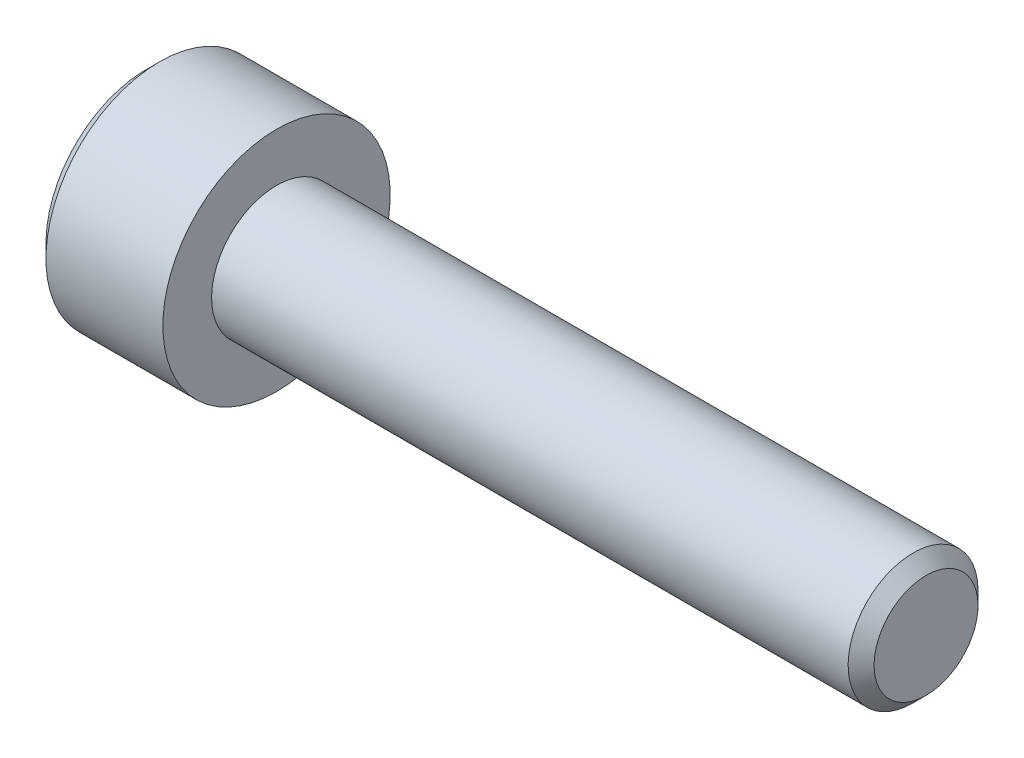
SolidWorks part; units mm, degrees
ref_plane "Front" through (0, 0, 0) normal (0, 0, 1) x (1, 0, 0)
ref_plane "Top" through (0, 0, 0) normal (0, 1, 0) x (1, 0, 0)
ref_plane "Right" through (0, 0, 0) normal (1, 0, 0) x (0, 0, -1)
ref_plane "Plane1" through (0, 0, 0) normal (0, 0, 1) x (1, 0, 0)
sketch "Sketch1" plane through (0, 0, 0) normal (0, 0, 1) x (1, 0, 0)
  line L0 (-4, 0) -> (-4, 3.1)
  line L1 (-4, 3.1) -> (-3.6, 3.5)
  line L2 (-3.6, 3.5) -> (0, 3.5)
  line L3 (0, 3.5) -> (0, 2)
  line L4 (0, 2) -> (20, 2)
  line L6 (20, 2) -> (20, 0)
  line L7 (20, 0) -> (-4, 0)
  line L8 (20, 0) -> (-4, 0) construction
  dimension "D1" = 20
  dimension "D2" = 4
  dimension "D3" = 2
  dimension "D4" = 3.5
revolve "Revolve1" add sketch "Sketch1" angle 360 about L8
ref_plane "Plane2" through (0, 0, 0) normal (0, 0, 1) x (1, 0, 0)
chamfer "Chamfer1" distance 0.4 angle 45 1 edges at (20, -2, 0)
sketch "Sketch2" plane through (0, 0, 0) normal (0, 0, 1) x (1, 0, 0)
  line L0 (-4, 0) -> (-4, 1.5)
  line L1 (-4, 1.5) -> (-2, 1.5)
  line L2 (-2, 1.5) -> (-1.5981, 0)
  line L3 (-1.5981, 0) -> (-4, 0)
  line L4 (-1.5981, 0) -> (-4, 0) construction
revolve "Cut-Revolve1" cut sketch "Sketch2" angle 360 about L4
ref_plane "Plane3" through (-4, 0, 0) normal (1, 0, 0) x (0, 0, -1)
sketch "Sketch3" plane through (-4, 0, 0) normal (1, 0, 0) x (0, 0, -1)
  line L0 (-1.5, 0.866) -> (-1.5, -0.866)
  line L1 (-1.5, -0.866) -> (0, -1.7321)
  line L2 (0, -1.7321) -> (1.5, -0.866)
  line L3 (1.5, -0.866) -> (1.5, 0.866)
  line L4 (1.5, 0.866) -> (0, 1.7321)
  line L5 (0, 1.7321) -> (-1.5, 0.866)
extrude "Cut-Extrude1" cut sketch "Sketch3" along normal blind 2
